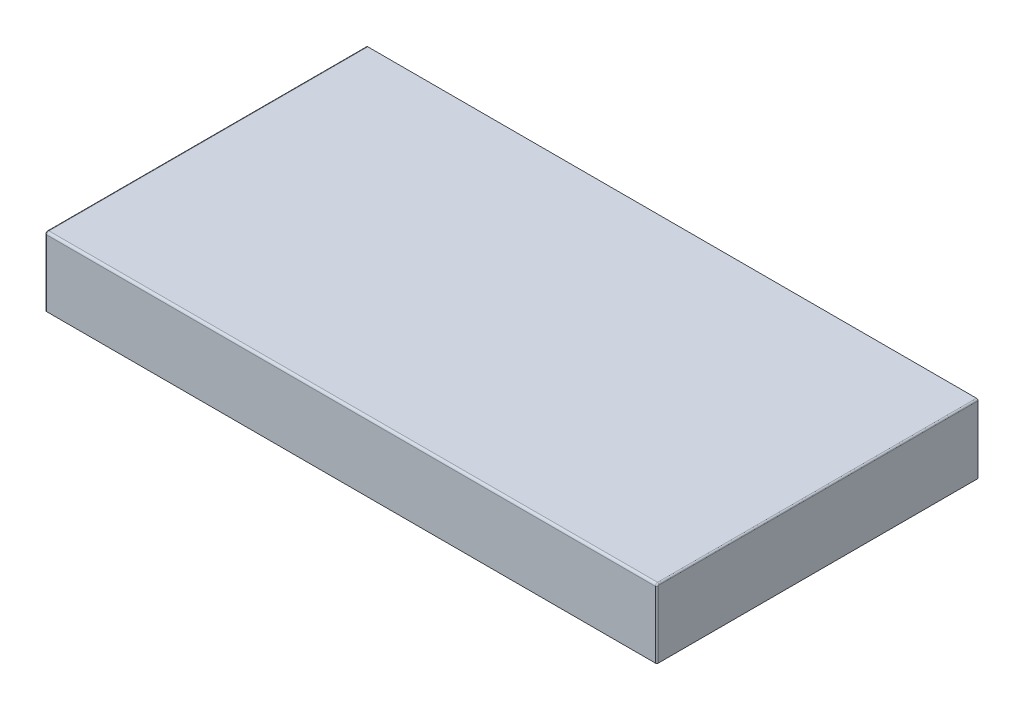
SolidWorks part; units mm, degrees
ref_plane "Plano frontal" through (0, 0, 0) normal (0, 0, 1) x (1, 0, 0)
ref_plane "Plano superior" through (0, 0, 0) normal (0, 1, 0) x (1, 0, 0)
ref_plane "Plano direito" through (0, 0, 0) normal (1, 0, 0) x (0, 0, -1)
sketch "Sketch2" plane through (0, 0, 0) normal (0, 0, 1) x (1, 0, 0)
  line L1 (-400, 45) -> (400, 45)
  line L2 (-400, 45) -> (-400, -45)
  line L3 (-400, -45) -> (400, -45)
  line L4 (400, 45) -> (400, -45)
  line L5 (-400, 45) -> (400, -45) construction
  line L6 (-400, -45) -> (400, 45) construction
  point P0 (0, 0)
  dimension "D1" = 800
  dimension "D2" = 90
extrude "Boss-Extrude1" add sketch "Sketch2" along normal mid plane 420
fillet "Fillet1" radius 3 1 edges at (0, 45, 210)
fillet "Fillet2" radius 2 6 edges at (-400, 45, -1.5) (400, 45, -1.5) (-400, 44.1213, 209.1213) (400, 44.1213, 209.1213) (-400, -1.5, 210) (400, -1.5, 210)
